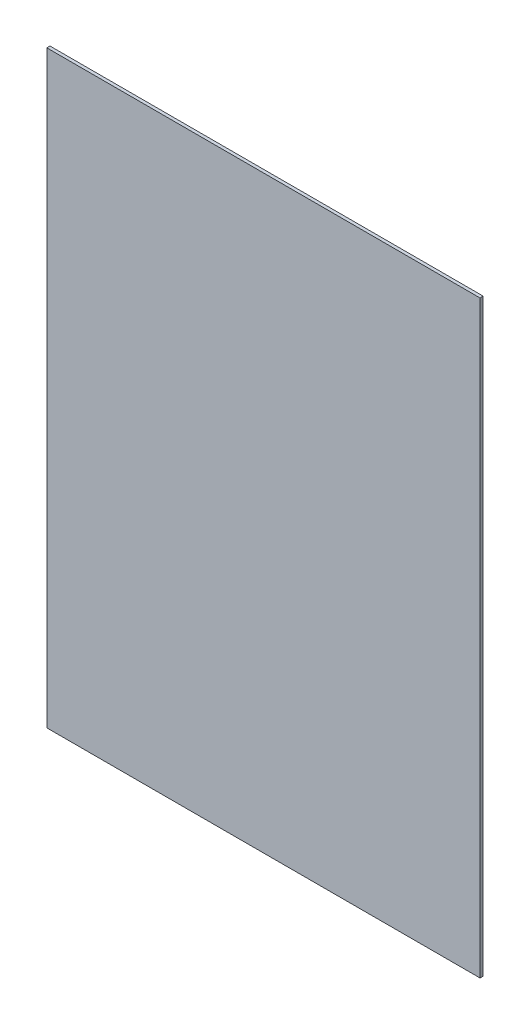
SolidWorks part; units mm, degrees
ref_plane "Front Plane" through (0, 0, 0) normal (0, 0, 1) x (1, 0, 0)
ref_plane "Top Plane" through (0, 0, 0) normal (0, 1, 0) x (1, 0, 0)
ref_plane "Right Plane" through (0, 0, 0) normal (1, 0, 0) x (0, 0, -1)
sketch "Sketch1" plane through (0, 0, 0) normal (0, 0, 1) x (1, 0, 0)
  line L1 (0, 0) -> (687, 0)
  line L2 (0, 0) -> (0, 934)
  line L3 (0, 934) -> (687, 934)
  line L4 (687, 0) -> (687, 934)
  dimension "D1" = 687
  dimension "D2" = 934
extrude "Boss-Extrude1" add sketch "Sketch1" along normal blind 5
